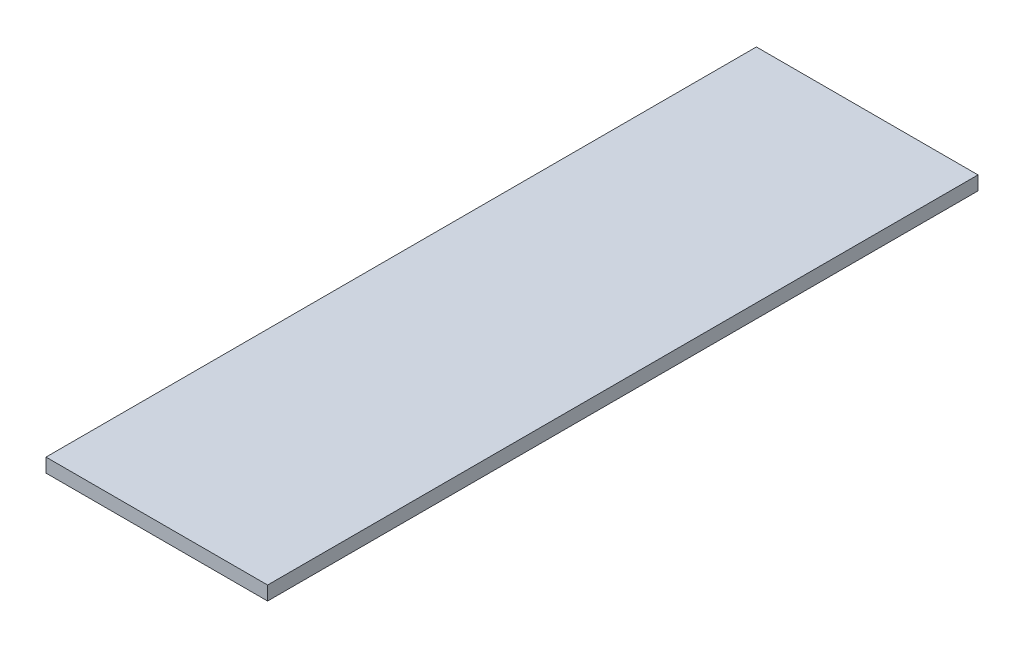
SolidWorks part; units mm, degrees
ref_plane "Спереди" through (0, 0, 0) normal (0, 0, 1) x (1, 0, 0)
ref_plane "Сверху" through (0, 0, 0) normal (0, 1, 0) x (1, 0, 0)
ref_plane "Справа" through (0, 0, 0) normal (1, 0, 0) x (0, 0, -1)
sketch "Эскиз1" plane through (0, 0, 0) normal (0, 1, 0) x (1, 0, 0)
  line L1 (143.5, -460) -> (-143.5, -460)
  line L2 (143.5, -460) -> (143.5, 460)
  line L3 (143.5, 460) -> (-143.5, 460)
  line L4 (-143.5, -460) -> (-143.5, 460)
  line L5 (143.5, -460) -> (-143.5, 460) construction
  line L6 (143.5, 460) -> (-143.5, -460) construction
  point P0 (0, 0)
  dimension "D1" = 920
  dimension "D2" = 287
extrude "Бобышка-Вытянуть1" add sketch "Эскиз1" along normal blind 18
